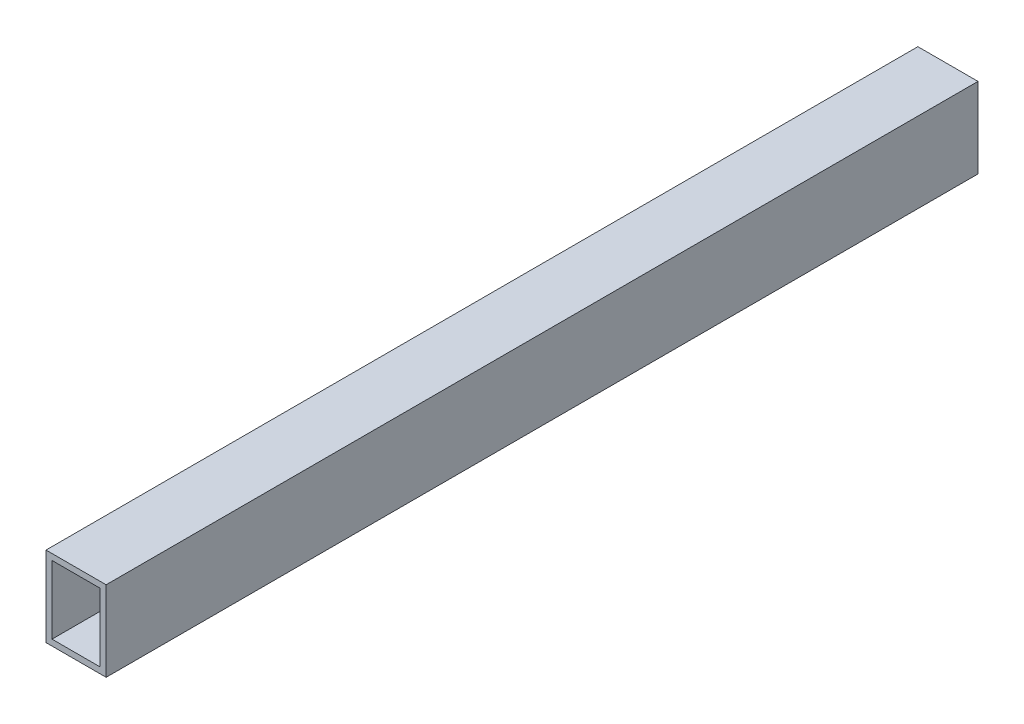
SolidWorks part; units mm, degrees
ref_plane "Front Plane" through (0, 0, 0) normal (0, 0, 1) x (1, 0, 0)
ref_plane "Top Plane" through (0, 0, 0) normal (0, 1, 0) x (1, 0, 0)
ref_plane "Right Plane" through (0, 0, 0) normal (1, 0, 0) x (0, 0, -1)
sketch "Croquis1" plane through (0, 0, 0) normal (1, 0, 0) x (0, 0, -1)
  line L0 (-217.5, -20) -> (-217.5, 20)
  line L1 (-217.5, -20) -> (217.5, -20)
  line L2 (-217.5, 20) -> (217.5, 20)
  line L3 (217.5, -20) -> (217.5, 20)
  line L4 (-217.5, -20) -> (217.5, 20) construction
  line L5 (-217.5, 20) -> (217.5, -20) construction
  point P1 (0, 0)
  dimension "D1" = 435
  dimension "D2" = 40
extrude "Saliente-Extruir1" add sketch "Croquis1" along normal blind 30
sketch "Croquis2" plane through (0, 0, 217.5) normal (0, 0, 1) x (1, 0, 0)
  line L0 (3, -17) -> (27, -17)
  line L1 (3, -17) -> (3, 17)
  line L2 (27, -17) -> (27, 17)
  line L3 (3, 17) -> (27, 17)
  line L4 (3, -17) -> (27, 17) construction
  line L5 (27, -17) -> (3, 17) construction
  line L6 (30, 20) -> (30, -20) construction
  line L7 (30, 20) -> (0, 20) construction
  line L8 (0, 20) -> (0, -20) construction
  line L9 (30, -20) -> (0, -20) construction
  point P1 (15, 0)
  dimension "D1" = 3
  dimension "D2" = 3
  dimension "D3" = 3
  dimension "D4" = 3
extrude "Cortar-Extruir1" cut sketch "Croquis2" against normal blind 890
